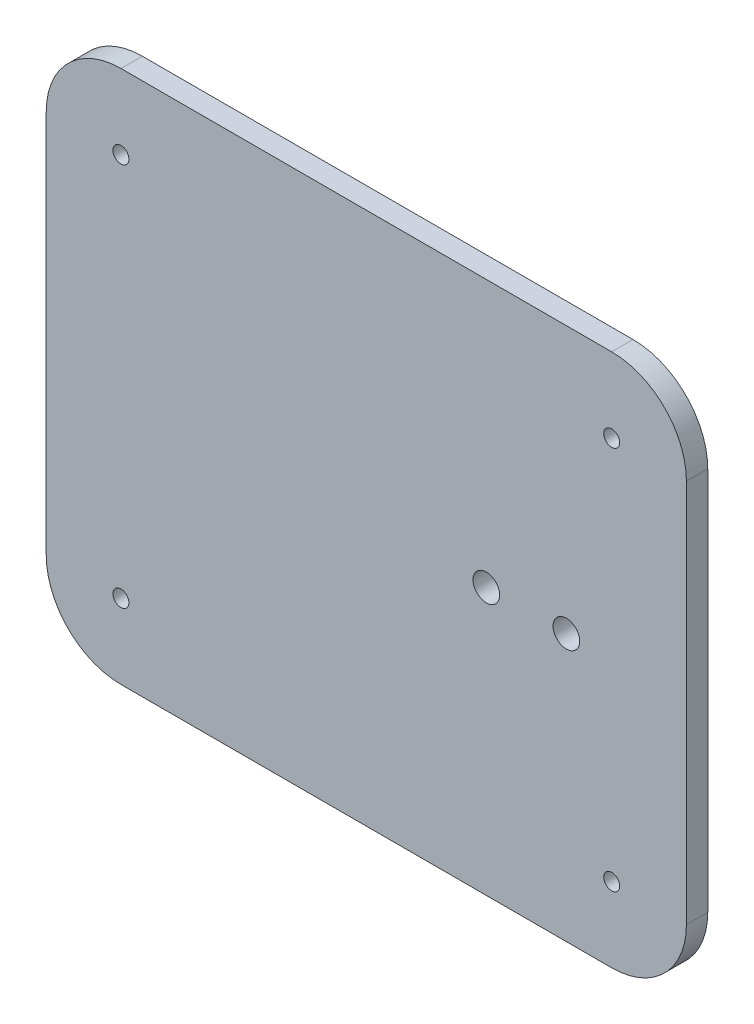
SolidWorks part; units mm, degrees
ref_plane "前视基准面" through (0, 0, 0) normal (0, 0, 1) x (1, 0, 0)
ref_plane "上视基准面" through (0, 0, 0) normal (0, 1, 0) x (1, 0, 0)
ref_plane "右视基准面" through (0, 0, 0) normal (1, 0, 0) x (0, 0, -1)
other "Configuration Table"
sketch "草图1" plane through (0, 0, 0) normal (0, 0, 1) x (1, 0, 0)
  line L1 (-52.6556, 38.8382) -> (67.3444, 38.8382)
  line L2 (-52.6556, 38.8382) -> (-52.6556, -61.1618)
  line L3 (-52.6556, -61.1618) -> (67.3444, -61.1618)
  line L4 (67.3444, 38.8382) -> (67.3444, -61.1618)
  dimension "D1" = 120
  dimension "D2" = 100
extrude "凸台-拉伸1" add sketch "草图1" along normal blind 4
fillet "圆角1" radius 14 4 edges at (67.3444, 38.8382, 2) (67.3444, -61.1618, 2) (-52.6556, -61.1618, 2) (-52.6556, 38.8382, 2)
sketch "草图2" plane through (0, 0, 4) normal (0, 0, 1) x (1, 0, 0)
  line L0 (-52.6556, 24.8382) -> (67.3444, 24.8382) construction
  line L1 (-38.6556, 38.8382) -> (-38.6556, -61.1618) construction
  line L2 (53.3444, -61.1618) -> (53.3444, 38.8382) construction
  line L3 (67.3444, -47.1618) -> (-52.6556, -47.1618) construction
  circle A0 centre (53.3444, 24.8382) radius 1.5
  circle A1 centre (-38.6556, 24.8382) radius 1.5
  circle A2 centre (-38.6556, -47.1618) radius 1.5
  circle A3 centre (53.3444, -47.1618) radius 1.5
  dimension "D1" = 3
extrude "切除-拉伸1" cut sketch "草图2" against normal through all
sketch "草图7" plane through (0, 0, 0) normal (0, 0, -1) x (-1, 0, 0)
  line L0 (-67.3444, -11.1618) -> (52.6556, -11.1618) construction
  line L1 (-67.3444, -47.1618) -> (-67.3444, 24.8382) construction
  line L2 (52.6556, 24.8382) -> (52.6556, -47.1618) construction
  circle A0 centre (-44.8444, -11.1618) radius 2.5
  circle A1 centre (-29.8444, -11.1618) radius 2.5
  dimension "D2" = 5
  dimension "D4" = 5
  dimension "D1" = 22.5
  dimension "D3" = 15
extrude "切除-拉伸2" cut sketch "草图7" against normal through all
